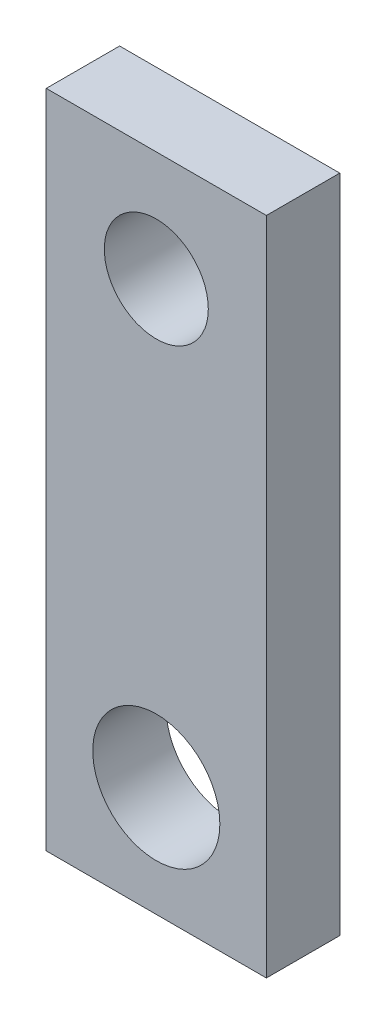
SolidWorks part; units mm, degrees
material "Copper"
ref_plane "Front" through (0, 0, 0) normal (0, 0, 1) x (1, 0, 0)
ref_plane "Top" through (0, 0, 0) normal (0, 1, 0) x (1, 0, 0)
ref_plane "Right" through (0, 0, 0) normal (1, 0, 0) x (0, 0, -1)
sketch "Sketch1" plane through (0, 0, 0) normal (0, 0, 1) x (1, 0, 0)
  line L1 (9.525, 89.931) -> (-9.525, 89.931)
  line L2 (9.525, 89.931) -> (9.525, 32.781)
  line L3 (9.525, 32.781) -> (-9.525, 32.781)
  line L4 (-9.525, 89.931) -> (-9.525, 32.781)
  line L5 (0, 80.406) -> (0, 42.306) construction
  line L6 (0, 80.406) -> (0, 42.306) construction
  point P6 (0, 89.931)
  dimension "D1" = 19.05
  dimension "D2" = 9.525
  dimension "D3" = 9.525
extrude "Boss-Extrude1" add sketch "Sketch1" along normal blind 6.35
hole_wizard "M10 Clearance Hole1" positions "Sketch3" profile "Sketch4" hole size "M10" standard "ANSI Metric"
sketch "Sketch3" plane through (0, 0, 6.35) normal (0, 0, 1) x (1, 0, 0)
  point P2 (0, 42.306)
  point P5 (0, 0)
  point P7 (0, 0)
  point P9 (0, 0)
sketch "Sketch4" plane through (0, 42.306, 6.35) normal (1, 0, 0) x (0, -1, 0)
  line L0 (0, 0) -> (0, 28.7047)
  line L1 (0, 28.7047) -> (5.5, 25.4)
  line L2 (5.5, 25.4) -> (5.5, 0)
  line L5 (5.5, 0) -> (0, 0)
  line L10 (0, 28.7047) -> (-5.5, 25.4) construction
  line L11 (0, -6.35) -> (0, 107.95) construction
  dimension "Hole Dia." = 11
  dimension "Hole Depth" = 25.4
  dimension "Drill Angle" = 118
hole_wizard "M8 Clearance Hole2" positions "Sketch5" profile "Sketch6" hole size "M8" standard "ANSI Metric"
sketch "Sketch5" plane through (0, 0, 6.35) normal (0, 0, 1) x (1, 0, 0)
  point P0 (0, 80.406)
  point P3 (0, 0)
sketch "Sketch6" plane through (0, 80.406, 6.35) normal (1, 0, 0) x (0, -1, 0)
  line L0 (0, 0) -> (0, 28.1039)
  line L1 (0, 28.1039) -> (4.5, 25.4)
  line L2 (4.5, 25.4) -> (4.5, 0)
  line L5 (4.5, 0) -> (0, 0)
  line L10 (0, 28.1039) -> (-4.5, 25.4) construction
  line L11 (0, -6.35) -> (0, 107.95) construction
  dimension "Hole Dia." = 9
  dimension "Hole Depth" = 25.4
  dimension "Drill Angle" = 118
